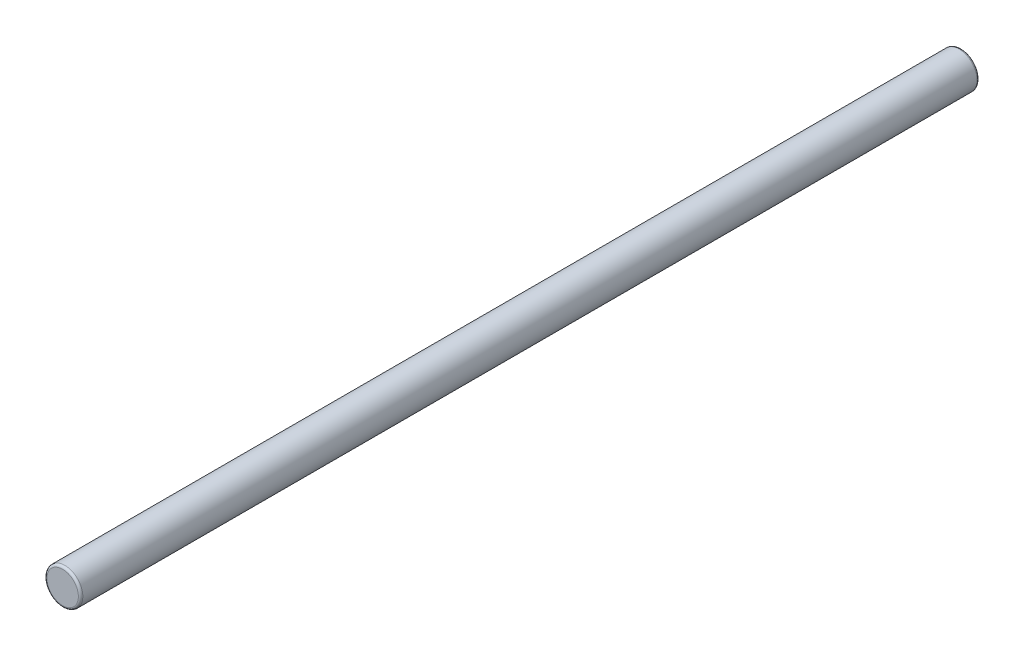
SolidWorks part; units mm, degrees
ref_plane "Front Plane" through (0, 0, 0) normal (0, 0, 1) x (1, 0, 0)
ref_plane "Top Plane" through (0, 0, 0) normal (0, 1, 0) x (1, 0, 0)
ref_plane "Right Plane" through (0, 0, 0) normal (1, 0, 0) x (0, 0, -1)
sketch "Sketch1" plane through (0, 0, 0) normal (0, 0, 1) x (1, 0, 0)
  circle A0 centre (0, 0) radius 4
  dimension "D1" = 8
extrude "Boss-Extrude1" add sketch "Sketch1" along normal blind 200 contours A0
fillet "Fillet1" radius 0.5 2 edges at (4, 0, 0) (4, 0, 200)
